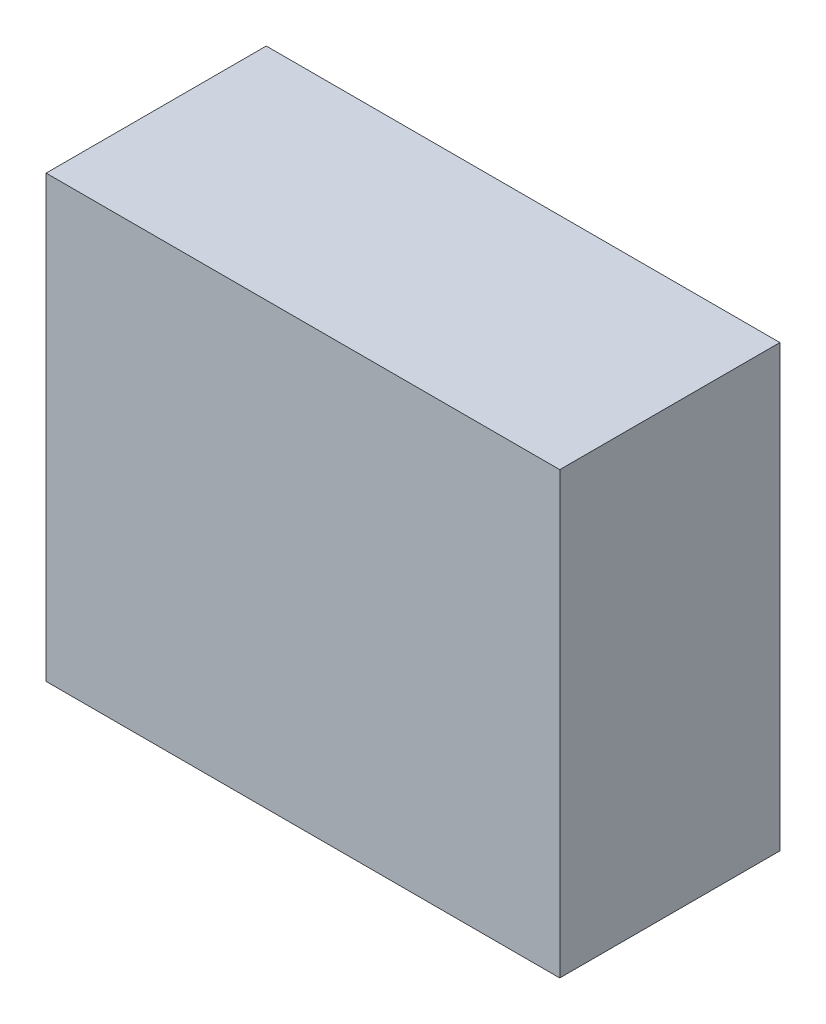
SolidWorks part; units mm, degrees
ref_plane "Front Plane" through (0, 0, 0) normal (0, 0, 1) x (1, 0, 0)
ref_plane "Top Plane" through (0, 0, 0) normal (0, 1, 0) x (1, 0, 0)
ref_plane "Right Plane" through (0, 0, 0) normal (1, 0, 0) x (0, 0, -1)
sketch "Sketch1" plane through (0, 0, 0) normal (0, 1, 0) x (1, 0, 0)
  line L1 (-88.9, -38.1) -> (88.9, -38.1)
  line L2 (-88.9, -38.1) -> (-88.9, 38.1)
  line L3 (-88.9, 38.1) -> (88.9, 38.1)
  line L4 (88.9, -38.1) -> (88.9, 38.1)
  line L5 (-88.9, -38.1) -> (88.9, 38.1) construction
  line L6 (-88.9, 38.1) -> (88.9, -38.1) construction
  point P0 (0, 0)
  dimension "D1" = 177.8
  dimension "D2" = 76.2
extrude "Boss-Extrude1" add sketch "Sketch1" along normal blind 152.4
